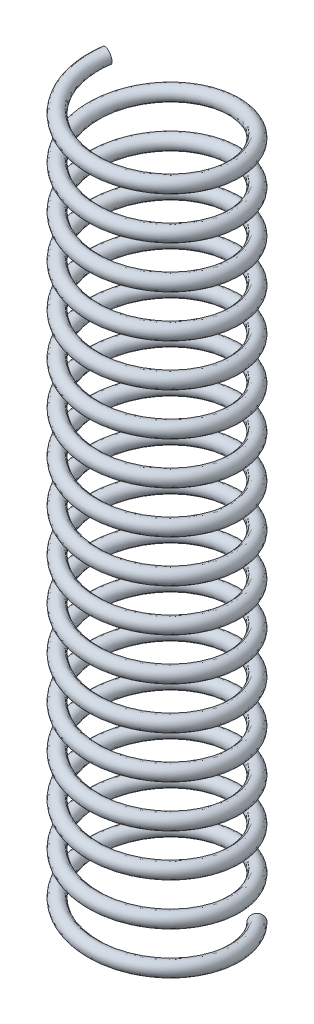
SolidWorks part; units mm, degrees
ref_plane "Front Plane" through (0, 0, 0) normal (0, 0, 1) x (1, 0, 0)
ref_plane "Top Plane" through (0, 0, 0) normal (0, 1, 0) x (1, 0, 0)
ref_plane "Right Plane" through (0, 0, 0) normal (1, 0, 0) x (0, 0, -1)
sketch "Sketch1" plane through (0, 0, 0) normal (0, 1, 0) x (1, 0, 0)
  circle A0 centre (0, 0) radius 5
  dimension "D1" = 10
curve "Helix/Spiral1" pitch 3 height 50 turns 16.6667
sweep "Sweep1" add path "Helix/Spiral1" circular profile diameter 1 parameters "D3"=1
ref_plane "Plane2" through (0, 0, 0) normal (0, 0, 1) x (1, 0, 0)
sketch "Sketch6" plane through (0, 0, 0) normal (0, 0, 1) x (1, 0, 0)
  line L0 (0, 53.1469) -> (0, -2.9038) construction
